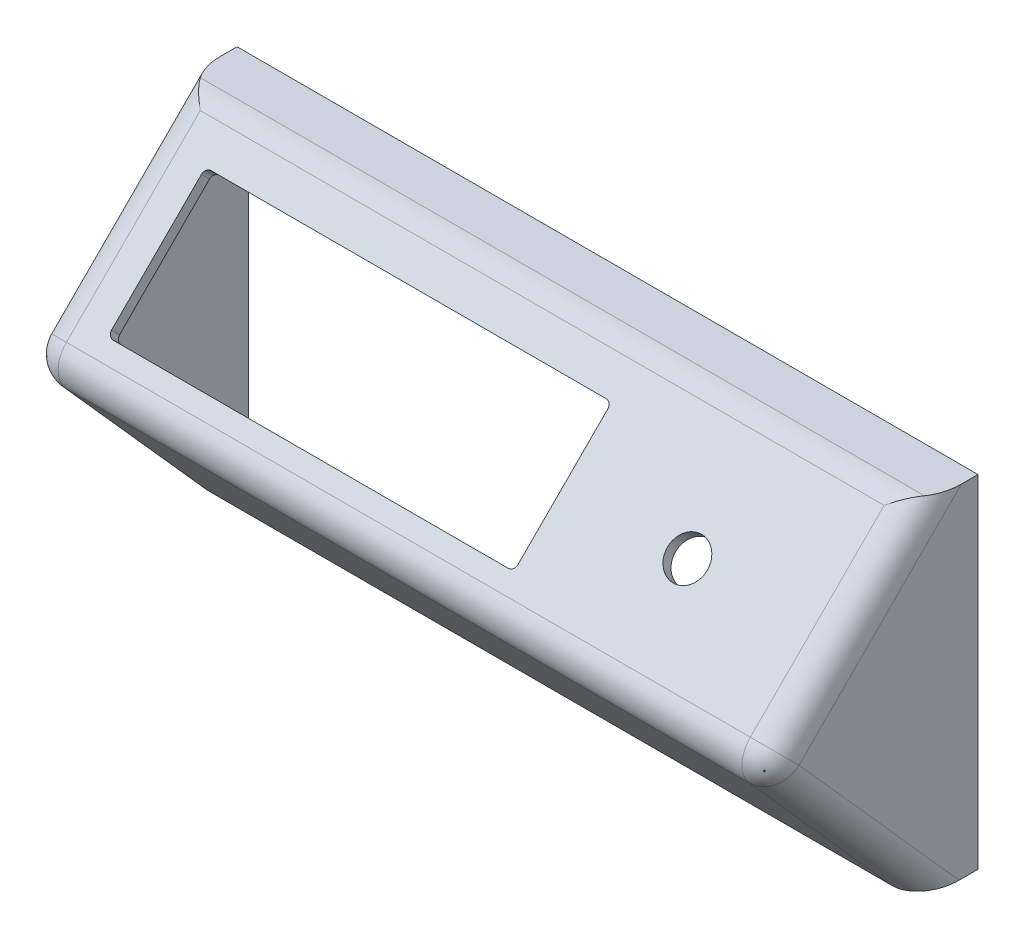
SolidWorks part; units mm, degrees
material "PTFE (general)"
ref_plane "Front Plane" through (0, 0, 0) normal (0, 0, 1) x (1, 0, 0)
ref_plane "Top Plane" through (0, 0, 0) normal (0, 1, 0) x (1, 0, 0)
ref_plane "Right Plane" through (0, 0, 0) normal (1, 0, 0) x (0, 0, -1)
sketch "Sketch1" plane through (0, 0, 0) normal (1, 0, 0) x (0, 0, -1)
  line L1 (0, 60) -> (-28.2843, 31.7157)
  line L2 (-28.2843, 31.7157) -> (0, 0)
  line L4 (0, 60) -> (10, 60)
  line L6 (0, 0) -> (10, 0)
  line L7 (10, 60) -> (10, 0)
  point P3 (0, 0)
  point P7 (-17.8719, 31.7157)
  dimension "D1" = 40
  dimension "D2" = 10
  dimension "D3" = 60
  dimension "D4" = 135
extrude "Boss-Extrude1" add sketch "Sketch1" along normal mid plane 130
shell "Shell1" thickness 2
sketch "Sketch2" plane through (0, 30, 30) normal (0, 0.7071, 0.7071) x (1, 0, 0)
  line L1 (15.3, 10.2764) -> (-54, 10.2764)
  line L2 (16.3, 11.2764) -> (16.3, 33.5764)
  line L3 (15.3, 34.5764) -> (-54, 34.5764)
  line L4 (-55, 11.2764) -> (-55, 33.5764)
  line L5 (16.3, 10.2764) -> (-55, 34.5764) construction
  line L6 (16.3, 34.5764) -> (-55, 10.2764) construction
  line L7 (-65, 42.4264) -> (-65, 2.4264) construction
  line L8 (-65, 22.4264) -> (65, 22.4264) construction
  line L9 (65, 42.4264) -> (65, 2.4264) construction
  arc A0 (16.3, 33.5764) -> (15.3, 34.5764) centre (15.3, 33.5764) ccw
  arc A1 (15.3, 10.2764) -> (16.3, 11.2764) centre (15.3, 11.2764) ccw
  arc A2 (-54, 10.2764) -> (-55, 11.2764) centre (-54, 11.2764) cw
  arc A3 (-54, 34.5764) -> (-55, 33.5764) centre (-54, 33.5764) ccw
  point P0 (-19.35, 22.4264)
  point P14 (0, 0)
  dimension "D3" = 1
  dimension "D1" = 71.3
  dimension "D2" = 24.3
  dimension "D4" = 10
extrude "Cut-Extrude1" cut sketch "Sketch2" against normal blind 100
fillet "Fillet1" radius 5 6 edges at (65, 15.8579, 14.1421) (0, 60, 0) (-65, 15.8579, 14.1421) (-65, 45.8579, 14.1421) (65, 45.8579, 14.1421) (0, 31.7157, 28.2843)
sketch "Sketch3" plane through (0, 30, 30) normal (0, 0.7071, 0.7071) x (1, 0, 0)
  line L1 (-65, 22.4264) -> (65, 22.4264) construction
  line L2 (16.3, 11.2764) -> (16.3, 33.5764) construction
  circle A0 centre (38.15, 22.4264) radius 3.5
  point P4 (0, 0)
  point P5 (0, 0)
  point P6 (0, 0)
  dimension "D1" = 7
  dimension "D2" = 21.85
extrude "Cut-Extrude2" cut sketch "Sketch3" against normal blind 100
